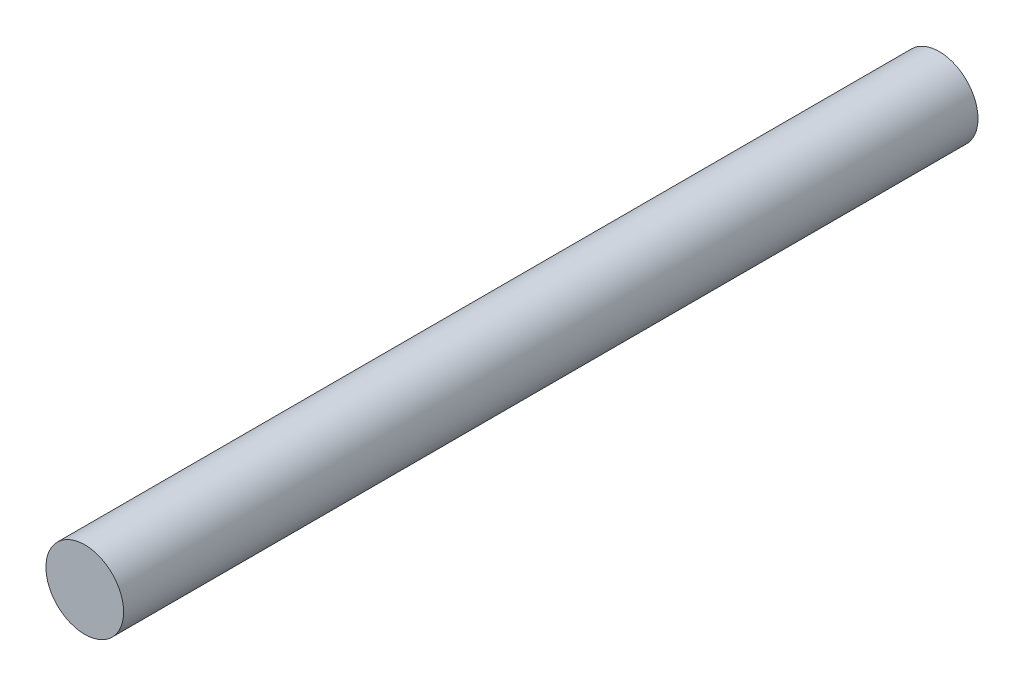
SolidWorks part; units mm, degrees
ref_plane "Front Plane" through (0, 0, 0) normal (0, 0, 1) x (1, 0, 0)
ref_plane "Top Plane" through (0, 0, 0) normal (0, 1, 0) x (1, 0, 0)
ref_plane "Right Plane" through (0, 0, 0) normal (1, 0, 0) x (0, 0, -1)
sketch "Sketch1" plane through (0, 0, 0) normal (0, 0, 1) x (1, 0, 0)
  circle A0 centre (0, -2.0323) radius 25.4
extrude "Boss-Extrude1" add sketch "Sketch1" along normal blind 558.8
